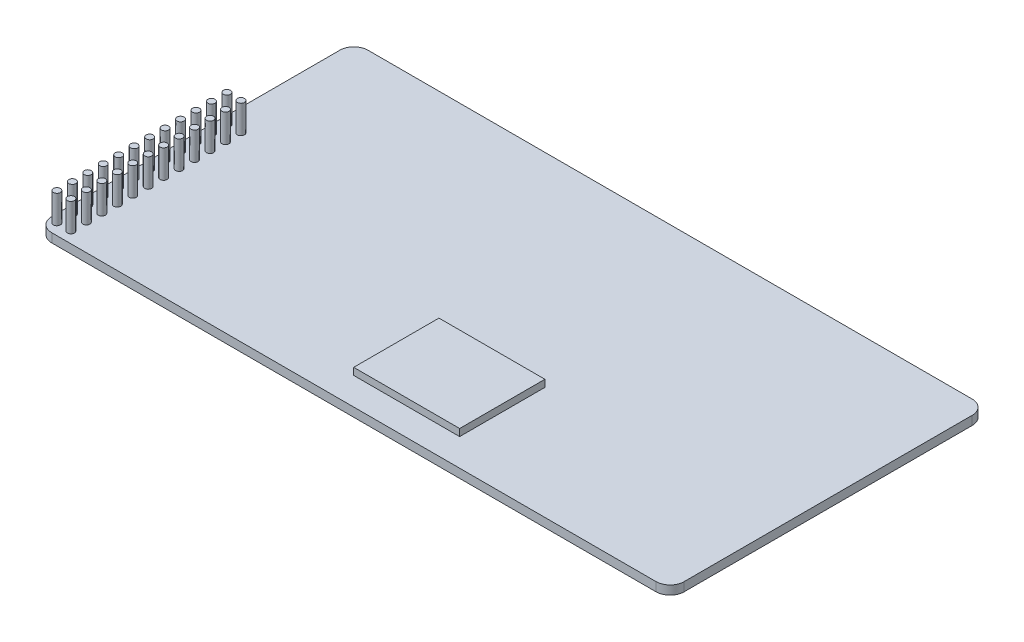
SolidWorks part; units mm, degrees
ref_plane "Front Plane" through (0, 0, 0) normal (0, 0, 1) x (1, 0, 0)
ref_plane "Top Plane" through (0, 0, 0) normal (0, 1, 0) x (1, 0, 0)
ref_plane "Right Plane" through (0, 0, 0) normal (1, 0, 0) x (0, 0, -1)
sketch "Sketch1" plane through (0, 0, 0) normal (0, 1, 0) x (1, 0, 0)
  line L1 (-55.88, -28.575) -> (49.53, -28.575)
  line L2 (-57.15, -22.225) -> (-57.15, 28.575)
  line L3 (-57.15, 28.575) -> (57.15, 28.575)
  line L4 (57.15, -22.225) -> (57.15, 28.575)
  line L5 (-57.15, -28.575) -> (57.15, 28.575) construction
  line L6 (-57.15, 28.575) -> (57.15, -28.575) construction
  line L7 (-57.15, -28.575) -> (-55.88, -28.575)
  line L8 (-57.15, -28.575) -> (-57.15, -22.225)
  line L11 (57.15, -28.575) -> (49.53, -28.575)
  line L12 (57.15, -28.575) -> (57.15, -22.225)
  point P0 (0, 0)
  point P12 (0, 0)
  point P13 (0, 0)
  point P14 (0, 0)
  point P15 (0, 0)
  dimension "D1" = 114.3
  dimension "D2" = 57.15
extrude "Extrude1" add sketch "Sketch1" along normal blind 1.6002
fillet "Fillet1" radius 2.54 4 edges at (57.15, 0.8001, 28.575) (57.15, 0.8001, -28.575) (-57.15, 0.8001, -28.575) (-57.15, 0.8001, 28.575)
sketch "Sketch2" plane through (0, 1.6002, 0) normal (0, 1, 0) x (1, 0, 0)
  line L1 (-4.986, -8.2156) -> (14.1648, -8.2156)
  line L2 (-4.986, -8.2156) -> (-4.986, -23.6269)
  line L3 (-4.986, -23.6269) -> (14.1648, -23.6269)
  line L4 (14.1648, -8.2156) -> (14.1648, -23.6269)
extrude "Extrude2" add sketch "Sketch2" along normal blind 1.27 separate body
sketch "Sketch3" plane through (0, 1.6002, 0) normal (0, 1, 0) x (1, 0, 0)
  circle A0 centre (-55.6873, 4.1556) radius 0.635
  circle A1 centre (-53.1473, 4.1556) radius 0.635
  circle A2 centre (-55.6873, 1.3616) radius 0.635
  circle A3 centre (-53.1473, 1.3616) radius 0.635
  circle A4 centre (-55.6873, -1.4324) radius 0.635
  circle A5 centre (-53.1473, -1.4324) radius 0.635
  circle A6 centre (-55.6873, -4.2264) radius 0.635
  circle A7 centre (-53.1473, -4.2264) radius 0.635
  circle A8 centre (-55.6873, -7.0204) radius 0.635
  circle A9 centre (-53.1473, -7.0204) radius 0.635
  circle A10 centre (-55.6873, -9.8144) radius 0.635
  circle A11 centre (-53.1473, -9.8144) radius 0.635
  circle A12 centre (-55.6873, -12.6084) radius 0.635
  circle A13 centre (-53.1473, -12.6084) radius 0.635
  circle A14 centre (-55.6873, -15.4024) radius 0.635
  circle A15 centre (-53.1473, -15.4024) radius 0.635
  circle A16 centre (-55.6873, -18.1964) radius 0.635
  circle A17 centre (-53.1473, -18.1964) radius 0.635
  circle A18 centre (-55.6873, -20.9904) radius 0.635
  circle A19 centre (-53.1473, -20.9904) radius 0.635
  circle A20 centre (-55.6873, -23.7844) radius 0.635
  circle A21 centre (-53.1473, -23.7844) radius 0.635
  circle A22 centre (-55.6873, -26.5784) radius 0.635
  circle A23 centre (-53.1473, -26.5784) radius 0.635
  dimension "D1" = 1.27
extrude "Extrude3" add sketch "Sketch3" along normal blind 5.08 separate body
